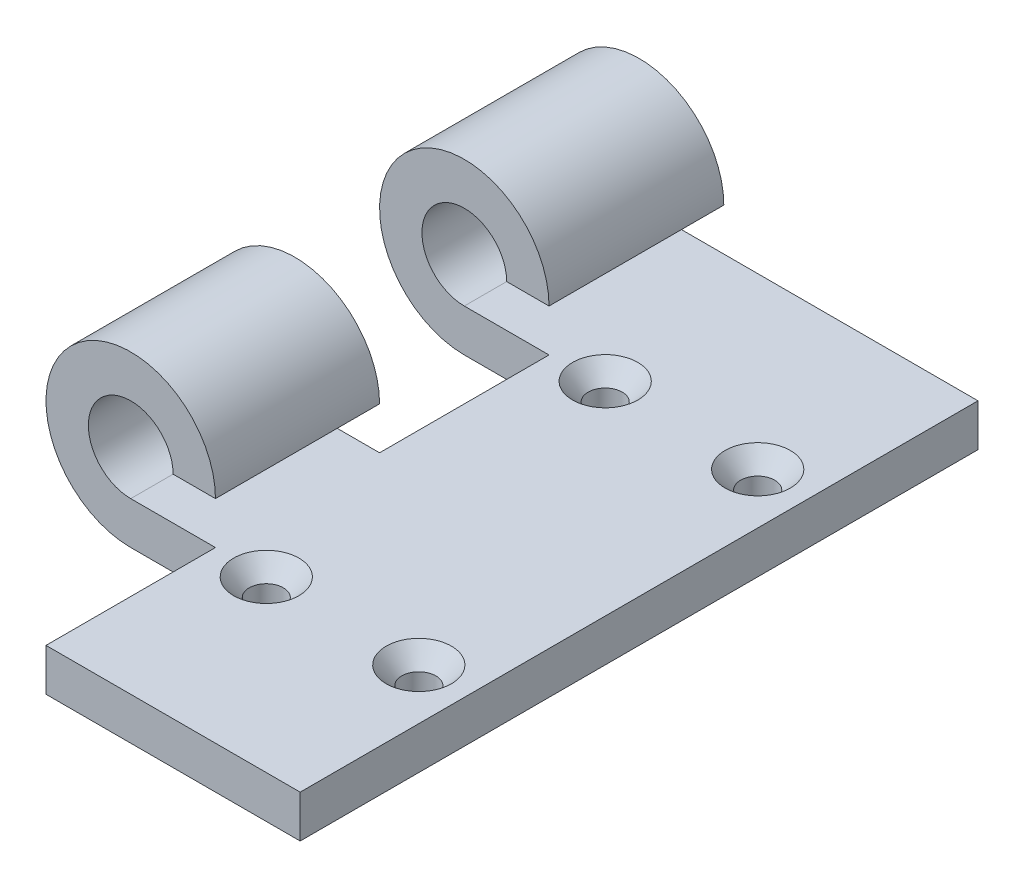
SolidWorks part; units mm, degrees
ref_plane "Front Plane" through (0, 0, 0) normal (0, 0, 1) x (1, 0, 0)
ref_plane "Top Plane" through (0, 0, 0) normal (0, 1, 0) x (1, 0, 0)
ref_plane "Right Plane" through (0, 0, 0) normal (1, 0, 0) x (0, 0, -1)
sketch "Sketch1" plane through (0, 0, 0) normal (0, 0, 1) x (1, 0, 0)
  line L0 (0, 0) -> (-50.8, 0)
  arc A0 (-50.8, 0) -> (-38.1, 12.7) centre (-50.8, 12.7) cw
  point P5 (-38.1, 12.7)
  dimension "D2" = 12.7
  dimension "D1" = 50.8
extrude "Extrude-Thin1" add sketch "Sketch1" along normal mid plane 101.6 thin
sketch "Sketch3" plane through (0, 6.35, 0) normal (0, 1, 0) x (1, 0, 0)
  line L1 (-63.5, -50.8) -> (-38.1, -50.8)
  line L2 (-63.5, -50.8) -> (-63.5, -25.4)
  line L3 (-63.5, -25.4) -> (-38.1, -25.4)
  line L4 (-38.1, -50.8) -> (-38.1, -25.4)
  dimension "D1" = 25.4
  dimension "D2" = 25.4
extrude "Cut-Extrude2" cut sketch "Sketch3" against normal through all both and the other way through all
pattern_linear "LPattern1" count 2 spacing 50 along (0, 0, -1) of "Cut-Extrude2"
hole_wizard "CSK for #10 Flat Head Machine Screw1" positions "Sketch4" profile "Sketch5" countersink size "#10" standard "ANSI Inch" end condition through all
sketch "Sketch4" plane through (0, 6.35, 0) normal (0, 1, 0) x (1, 0, 0)
  line L0 (0, 50.8) -> (-50.8, 50.8) construction
  line L1 (-38.1, 24.6) -> (-38.1, -0.8) construction
  point P0 (-30.48, 25.4)
  dimension "D1" = 25.4
  dimension "D2" = 7.62
sketch "Sketch5" plane through (-30.48, 6.35, -25.4) normal (1, 0, 0) x (0, 0, 1)
  line L0 (0, 0) -> (0, 6.35)
  line L1 (0, 6.35) -> (2.5527, 6.35)
  line L2 (2.5527, 6.35) -> (2.5527, 2.6882)
  line L3 (2.5527, 2.6882) -> (4.8895, 0)
  line L5 (4.8895, 0) -> (0, 0)
  line L6 (-2.5527, 2.6882) -> (-4.8895, 0) construction
  line L11 (0, -6.35) -> (0, 107.95) construction
  dimension "Thru Hole Dia." = 5.1054
  dimension "Thru Hole Depth" = 6.35
  dimension "Near C'Sink Dia." = 9.779
  dimension "Near C'Sink Angle" = 82
pattern_linear "LPattern2" count 2 spacing 50.8 along (0, 0, 1) count 2 spacing 22.86 along (1, 0, 0) of "CSK for #10 Flat Head Machine Screw1"
